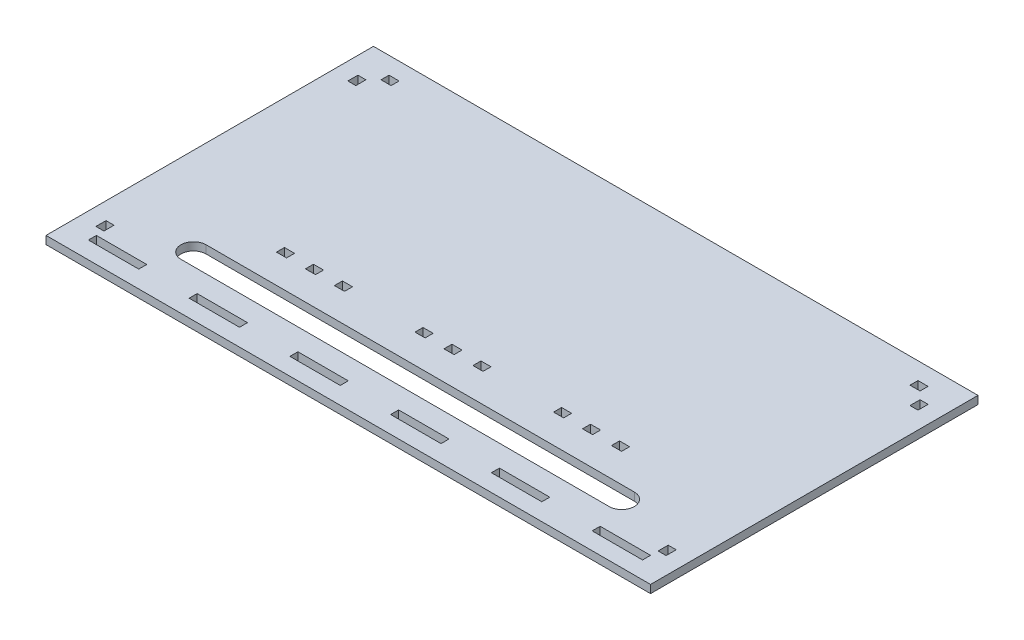
SolidWorks part; units mm, degrees
ref_plane "Front Plane" through (0, 0, 0) normal (0, 0, 1) x (1, 0, 0)
ref_plane "Top Plane" through (0, 0, 0) normal (0, 1, 0) x (1, 0, 0)
ref_plane "Right Plane" through (0, 0, 0) normal (1, 0, 0) x (0, 0, -1)
sketch "Sketch1" plane through (0, 0, 0) normal (0, 1, 0) x (1, 0, 0)
  line L0 (0, 65) -> (0, -65) construction
  line L1 (-120, 65) -> (120, 65)
  line L2 (-120, 65) -> (-120, -65)
  line L3 (-120, -65) -> (120, -65)
  line L4 (120, 65) -> (120, -65)
  line L5 (-111.5875, 55) -> (-111.5875, 45) construction
  line L6 (-113.175, 55) -> (-110, 55) construction
  line L7 (-113.175, 55) -> (-113.175, 45) construction
  line L8 (-113.175, 45) -> (-110, 45) construction
  line L9 (-110, 55) -> (-110, 45) construction
  line L10 (-110, 58.175) -> (-100, 58.175) construction
  line L11 (-110, 58.175) -> (-110, 55) construction
  line L12 (-110, 55) -> (-100, 55) construction
  line L13 (-100, 58.175) -> (-100, 55) construction
  line L14 (-110, 56.5875) -> (-100, 56.5875) construction
  line L15 (100, 56.5875) -> (110, 56.5875) construction
  line L16 (-113.175, 52) -> (-110, 52)
  line L17 (-113.175, 52) -> (-113.175, 48)
  line L18 (-113.175, 48) -> (-110, 48)
  line L19 (-110, 52) -> (-110, 48)
  line L20 (-113.175, 52) -> (-110, 48) construction
  line L21 (-113.175, 48) -> (-110, 52) construction
  line L22 (-107, 55) -> (-103, 55)
  line L23 (-107, 55) -> (-107, 58.175)
  line L24 (-107, 58.175) -> (-103, 58.175)
  line L25 (-103, 55) -> (-103, 58.175)
  line L26 (-107, 55) -> (-103, 58.175) construction
  line L27 (-107, 58.175) -> (-103, 55) construction
  line L28 (110, 55) -> (113.175, 55) construction
  line L29 (110, 55) -> (110, 45) construction
  line L30 (110, 45) -> (113.175, 45) construction
  line L31 (113.175, 55) -> (113.175, 45) construction
  line L32 (100, 58.175) -> (110, 58.175) construction
  line L33 (100, 58.175) -> (100, 55) construction
  line L34 (100, 55) -> (110, 55) construction
  line L35 (110, 58.175) -> (110, 55) construction
  line L36 (111.5875, 55) -> (111.5875, 45) construction
  line L37 (-111.5875, -45) -> (-111.5875, -55) construction
  line L38 (103, 55) -> (107, 55)
  line L39 (103, 55) -> (103, 58.175)
  line L40 (103, 58.175) -> (107, 58.175)
  line L41 (107, 55) -> (107, 58.175)
  line L42 (103, 55) -> (107, 58.175) construction
  line L43 (103, 58.175) -> (107, 55) construction
  line L44 (110, 52) -> (113.175, 52)
  line L45 (110, 52) -> (110, 48)
  line L46 (110, 48) -> (113.175, 48)
  line L47 (113.175, 52) -> (113.175, 48)
  line L48 (110, 52) -> (113.175, 48) construction
  line L49 (110, 48) -> (113.175, 52) construction
  line L50 (-113.175, -45) -> (-110, -45) construction
  line L51 (-113.175, -45) -> (-113.175, -55) construction
  line L52 (-113.175, -55) -> (-110, -55) construction
  line L53 (-110, -45) -> (-110, -55) construction
  line L54 (111.5875, -45) -> (111.5875, -55) construction
  line L55 (-113.175, -52) -> (-110, -52)
  line L56 (-113.175, -52) -> (-113.175, -48)
  line L57 (-113.175, -48) -> (-110, -48)
  line L58 (-110, -52) -> (-110, -48)
  line L59 (-113.175, -52) -> (-110, -48) construction
  line L60 (-113.175, -48) -> (-110, -52) construction
  line L61 (113.175, -55) -> (110, -55) construction
  line L62 (113.175, -55) -> (113.175, -45) construction
  line L63 (113.175, -45) -> (110, -45) construction
  line L64 (110, -55) -> (110, -45) construction
  line L65 (-70, -58.175) -> (-50, -58.175)
  line L66 (110, -52) -> (113.175, -52)
  line L67 (110, -52) -> (110, -48)
  line L68 (110, -48) -> (113.175, -48)
  line L69 (113.175, -52) -> (113.175, -48)
  line L70 (110, -52) -> (113.175, -48) construction
  line L71 (110, -48) -> (113.175, -52) construction
  line L72 (-110, -55) -> (-90, -55)
  line L73 (-110, -55) -> (-110, -58.175)
  line L74 (-110, -58.175) -> (-90, -58.175)
  line L75 (-90, -55) -> (-90, -58.175)
  line L76 (-70, -55) -> (-70, -58.175)
  line L77 (-70, -55) -> (-50, -55)
  line L78 (-50, -55) -> (-50, -58.175)
  line L79 (-30, -58.175) -> (-10, -58.175)
  line L80 (-30, -55) -> (-30, -58.175)
  line L81 (-30, -55) -> (-10, -55)
  line L82 (-10, -55) -> (-10, -58.175)
  line L83 (10, -58.175) -> (30, -58.175)
  line L84 (10, -55) -> (10, -58.175)
  line L85 (10, -55) -> (30, -55)
  line L86 (30, -55) -> (30, -58.175)
  line L87 (50, -58.175) -> (70, -58.175)
  line L88 (50, -55) -> (50, -58.175)
  line L89 (50, -55) -> (70, -55)
  line L90 (70, -55) -> (70, -58.175)
  line L91 (90, -58.175) -> (110, -58.175)
  line L92 (90, -55) -> (90, -58.175)
  line L93 (90, -55) -> (110, -55)
  line L94 (110, -55) -> (110, -58.175)
  line L191 (-68.5, -21.825) -> (-64.5, -21.825)
  line L192 (-68.5, -21.825) -> (-68.5, -25)
  line L193 (-68.5, -25) -> (-64.5, -25)
  line L194 (-64.5, -21.825) -> (-64.5, -25)
  line L195 (-57, -21.825) -> (-53, -21.825)
  line L196 (-57, -21.825) -> (-57, -25)
  line L197 (-57, -25) -> (-53, -25)
  line L198 (-53, -21.825) -> (-53, -25)
  line L199 (-45.5, -21.825) -> (-41.5, -21.825)
  line L200 (-45.5, -21.825) -> (-45.5, -25)
  line L201 (-45.5, -25) -> (-41.5, -25)
  line L202 (-41.5, -21.825) -> (-41.5, -25)
  line L216 (41.5, -25) -> (45.5, -25)
  line L217 (41.5, -25) -> (41.5, -21.825)
  line L218 (41.5, -21.825) -> (45.5, -21.825)
  line L219 (45.5, -25) -> (45.5, -21.825)
  line L220 (53, -25) -> (57, -25)
  line L221 (53, -25) -> (53, -21.825)
  line L222 (53, -21.825) -> (57, -21.825)
  line L223 (57, -25) -> (57, -21.825)
  line L224 (64.5, -25) -> (68.5, -25)
  line L225 (64.5, -25) -> (64.5, -21.825)
  line L226 (64.5, -21.825) -> (68.5, -21.825)
  line L227 (68.5, -25) -> (68.5, -21.825)
  line L240 (-13.5, -21.825) -> (-9.5, -21.825)
  line L241 (-13.5, -21.825) -> (-13.5, -25)
  line L242 (-13.5, -25) -> (-9.5, -25)
  line L243 (-9.5, -21.825) -> (-9.5, -25)
  line L244 (-2, -25) -> (2, -25)
  line L245 (-2, -25) -> (-2, -21.825)
  line L246 (-2, -21.825) -> (2, -21.825)
  line L247 (2, -25) -> (2, -21.825)
  line L248 (9.5, -25) -> (13.5, -25)
  line L249 (9.5, -25) -> (9.5, -21.825)
  line L250 (9.5, -21.825) -> (13.5, -21.825)
  line L251 (13.5, -25) -> (13.5, -21.825)
  line L252 (-57, -25) -> (-33.85, -25)
  line L253 (-85, -36.4381) -> (-85, -46.4381) construction
  line L254 (-68.5, -21.825) -> (-64.5, -21.825)
  line L255 (-68.5, -21.825) -> (-68.5, -25)
  line L256 (-68.5, -25) -> (-64.5, -25)
  line L257 (-64.5, -21.825) -> (-64.5, -25)
  line L261 (-68.5, -25) -> (-64.5, -25)
  line L263 (-76.15, 17.3) -> (-33.85, -25) construction
  line L264 (-55, -3.85) -> (-33.85, 17.3) construction
  line L266 (-85, -36.4381) -> (85, -36.4381)
  line L269 (-57, -21.825) -> (-57, -25)
  line L270 (-68.5, -21.825) -> (-68.5, -25)
  line L271 (-68.5, -25) -> (-64.5, -25)
  line L272 (-64.5, -21.825) -> (-64.5, -25)
  line L273 (-41.5, -21.825) -> (-41.5, -25)
  line L274 (-41.5, -25) -> (-45.5, -25)
  line L275 (-45.5, -21.825) -> (-45.5, -25)
  line L276 (-57, -25) -> (-53, -25)
  line L277 (-53, -21.825) -> (-53, -25)
  line L278 (-85, -46.4381) -> (85, -46.4381)
  line L280 (-57, -21.825) -> (-53, -21.825)
  line L281 (-45.5, -21.825) -> (-41.5, -21.825)
  line L282 (-68.5, -21.825) -> (-64.5, -21.825)
  line L291 (-55, 17.3) -> (-55, -21.825) construction
  line L293 (85, -36.4381) -> (85, -46.4381) construction
  arc A0 (-85, -36.4381) -> (-85, -46.4381) centre (-85, -41.4381) ccw
  arc A1 (85, -36.4381) -> (85, -46.4381) centre (85, -41.4381) cw
  point P19 (-111.5875, 50)
  point P24 (-105, 56.5875)
  point P41 (105, 56.5875)
  point P46 (111.5875, 50)
  point P57 (-111.5875, -50)
  point P68 (111.5875, -50)
  point P77 (-55, -25)
  point P121 (55, -25)
  point P134 (0, -25)
  point P135 (-55, -25)
  point P166 (-55, -23.4125)
  dimension "D1" = 240
  dimension "D2" = 130
  dimension "D3" = 65
  dimension "D4" = 120
  dimension "D5" = 6.825
  dimension "D6" = 6.825
  dimension "D7" = 10
  dimension "D8" = 10
  dimension "D9" = 3.175
  dimension "D10" = 10
  dimension "D11" = 4
  dimension "D12" = 4
  dimension "D13" = 6.825
  dimension "D14" = 6.825
  dimension "D15" = 10
  dimension "D16" = 10
  dimension "D17" = 10
  dimension "D18" = 3.175
  dimension "D19" = 4
  dimension "D20" = 4
  dimension "D21" = 6.825
  dimension "D22" = 10
  dimension "D23" = 10
  dimension "D24" = 3.175
  dimension "D25" = 4
  dimension "D26" = 6.825
  dimension "D27" = 3.175
  dimension "D28" = 10
  dimension "D29" = 10
  dimension "D30" = 4
  dimension "D31" = 20
  dimension "D32" = 3.175
  dimension "D39" = 3.175
  dimension "D34" = 7.5
  dimension "D35" = 7.5
  dimension "D36" = 55
  dimension "D38" = 4
  dimension "D40" = 3.175
  dimension "D41" = 7.5
  dimension "D42" = 7.5
  dimension "D43" = 55
  dimension "D44" = 30
  dimension "D45" = 30
  dimension "D46" = 4
  dimension "D47" = 3.175
  dimension "D48" = 7.5
  dimension "D49" = 7.5
  dimension "D50" = 30
  dimension "D51" = 42.3
  dimension "D52" = 42.3
  dimension "D57" = 4
  dimension "D58" = 3.175
  dimension "D59" = 7.5
  dimension "D60" = 7.5
  dimension "D37" = 10
  dimension "D33" = 6
extrude "Boss-Extrude4" add sketch "Sketch1" along normal blind 3.175 contours L4 L1 L2 L3 L251 L248 L249 L250 L247 L244 L245 L246 L227 L224 L225 L226 L223 L220 L221 L222 L219 L216 L217 L218 L69 L66 L67 L68 L58 L55 L56 L57 L41 L38 L39 L40 L25 L22 L23 L24 L16 | L89 L90 L87 L88 | L85 L86 L83 L84
equation "\"stepper width\"=4.23"
equation "\"stepper hole disctance\"= 3.1"
equation "\"stepper hole diameter\"=0.34"
equation "\"stepper shaft hole\"=2.4"
equation "\"tooth width\"=0.4"
equation "\"tooth thickness\"=0.3175"
equation "\"tooth to side\"=0.75"
equation "\"motor chamber height\"= 6"
equation "\"enclosure length\"= 22"
equation "\"platform diameter\"= 9cm"
equation "\"teeth width\"=0.3175"
equation "\"teeth lenght\"=2"
equation "\"tower width\"=7.7"
equation "\"D1@Sketch1\"=\"enclosure length\"+2"
equation "\"D2@Sketch1\"=\"enclosure length\"/2+2"
equation "\"D3@Sketch1\"=\"enclosure length\"/4+1"
equation "\"D4@Sketch1\"=\"enclosure length\"/2+1"
equation "\"D5@Sketch1\"=1 - \"tooth thickness\""
equation "\"D6@Sketch1\"=1 - \"tooth thickness\""
equation "\"D9@Sketch1\"=\"teeth width\""
equation "\"support width\"=1"
equation "\"D10@Sketch1\"=\"support width\""
equation "\"D11@Sketch1\"=\"tooth width\""
equation "\"D12@Sketch1\"=\"tooth width\""
equation "\"D13@Sketch1\"=1 - \"tooth thickness\""
equation "\"D14@Sketch1\"=1 - \"tooth thickness\""
equation "\"D17@Sketch1\"=\"support width\""
equation "\"D18@Sketch1\"=\"tooth thickness\""
equation "\"D19@Sketch1\"=\"tooth width\""
equation "\"D20@Sketch1\"=\"tooth width\""
equation "\"D21@Sketch1\"=1 - \"tooth thickness\""
equation "\"D23@Sketch1\"=\"support width\""
equation "\"D24@Sketch1\"=\"tooth thickness\""
equation "\"D25@Sketch1\"=\"tooth width\""
equation "\"D26@Sketch1\"=1 - \"tooth thickness\""
equation "\"D27@Sketch1\"=\"tooth thickness\""
equation "\"D28@Sketch1\"=\"support width\""
equation "\"D30@Sketch1\"=\"tooth width\""
equation "\"D31@Sketch1\"=\"teeth lenght\""
equation "\"D32@Sketch1\"=\"tooth thickness\""
equation "\"trial hole spacing\"= 0.75"
equation "\"mounting distance\"= 4"
equation "\"D39@Sketch1\"=\"tooth thickness\""
equation "\"D34@Sketch1\"=\"tooth to side\""
equation "\"half belt distance\"=5.5"
equation "\"D36@Sketch1\"=\"half belt distance\""
equation "\"D38@Sketch1\"=\"tooth width\""
equation "\"D40@Sketch1\"=\"tooth thickness\""
equation "\"D41@Sketch1\"=\"tooth to side\""
equation "\"D42@Sketch1\"=\"tooth to side\""
equation "\"D43@Sketch1\"=\"half belt distance\""
equation "\"holder distance to wall\"=3"
equation "\"D44@Sketch1\"=\"holder distance to wall\""
equation "\"D45@Sketch1\"=\"holder distance to wall\""
equation "\"D46@Sketch1\"=\"tooth width\""
equation "\"D47@Sketch1\"=\"tooth thickness\""
equation "\"D48@Sketch1\"=\"tooth to side\""
equation "\"D49@Sketch1\"=\"tooth to side\""
equation "\"D50@Sketch1\"=\"holder distance to wall\""
equation "\"pusher hole width\"=1"
equation "\"D37@Sketch1\"=\"pusher hole width\""
